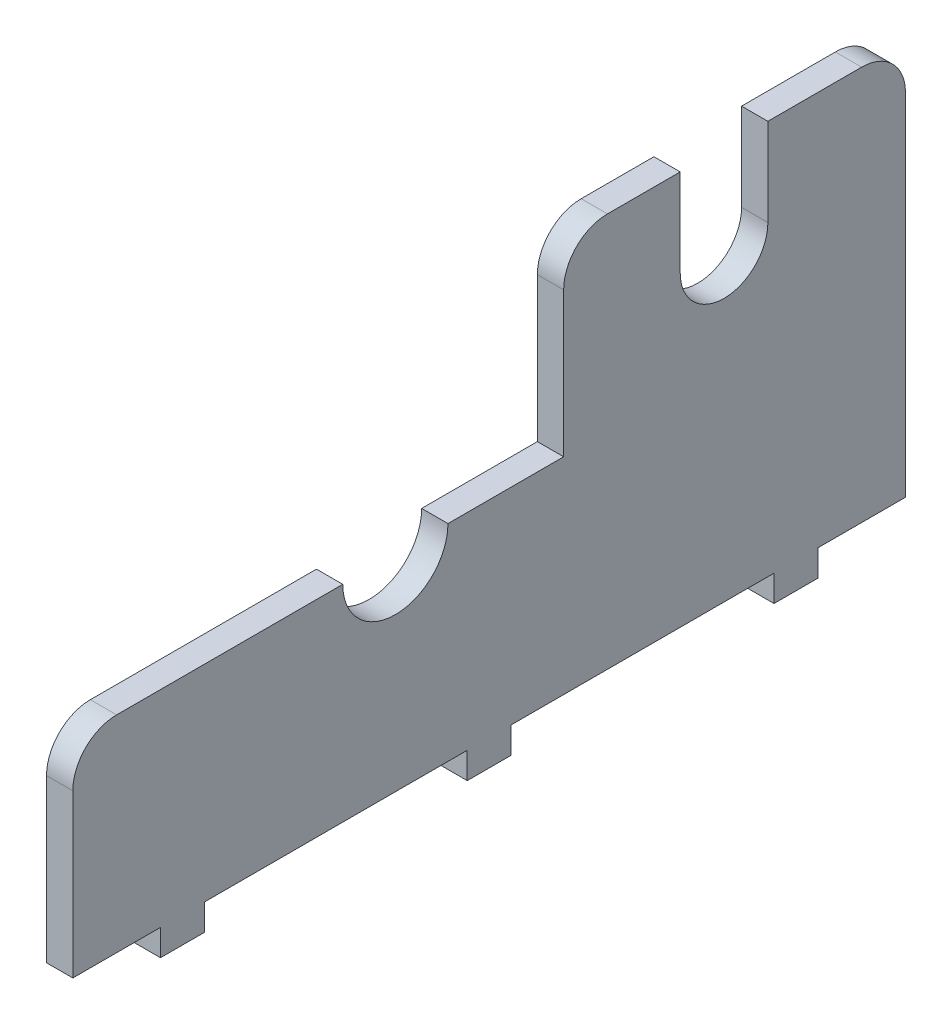
SolidWorks part; units mm, degrees
ref_plane "Front Plane" through (0, 0, 0) normal (0, 0, 1) x (1, 0, 0)
ref_plane "Top Plane" through (0, 0, 0) normal (0, 1, 0) x (1, 0, 0)
ref_plane "Right Plane" through (0, 0, 0) normal (1, 0, 0) x (0, 0, -1)
sketch "Sketch1" plane through (0, 0, 0) normal (1, 0, 0) x (0, 0, -1)
  line L0 (0, 55) -> (0, -55) construction
  line L1 (65, 0) -> (-30, 0)
  line L2 (65, 0) -> (65, 23.5)
  line L3 (65, 23.5) -> (-30, 23.5)
  line L4 (-30, 0) -> (-30, 23.5)
  line L5 (55, 0) -> (-55, 0) construction
  point P0 (0, 0)
  dimension "D2" = 30
  dimension "D1" = 95
  dimension "D4" = 23.5
extrude "Boss-Extrude1" add sketch "Sketch1" along normal blind 3
sketch "Sketch2" plane through (3, 0, 0) normal (1, 0, 0) x (0, 0, -1)
  line L0 (-30, 0) -> (65, 0) construction
  line L7 (-26.9862, 0) -> (-28.4862, -10) construction
  circle A0 centre (6.8, 23.5) radius 6
  point P6 (-28.4862, -10)
  point P11 (28.0724, -10)
  dimension "D1" = 12
  dimension "D3" = 6.8
  dimension "D2" = 23.5
extrude "Cut-Extrude1" cut sketch "Sketch2" against normal through all
sketch "Sketch4" plane through (0, 0, 0) normal (0, -1, 0) x (1, 0, 0)
  line L0 (3, 30) -> (3, -65) construction
  line L1 (3, 20) -> (0, 20)
  line L2 (3, 20) -> (3, 15)
  line L3 (3, 15) -> (0, 15)
  line L4 (0, 20) -> (0, 15)
  line L5 (0, 30) -> (0, -65) construction
  line L6 (3, 30) -> (0, 30) construction
  dimension "D1" = 5
  dimension "D2" = 10
extrude "Boss-Extrude2" add sketch "Sketch4" along normal blind 3
sketch "Sketch9" plane through (0, 23.5, 0) normal (0, 1, 0) x (1, 0, 0)
  line L0 (3, -30) -> (0, -30) construction
  line L1 (0, 26) -> (3, 26)
  line L2 (0, 26) -> (0, 65)
  line L3 (0, 65) -> (3, 65)
  line L4 (3, 26) -> (3, 65)
  dimension "D1" = 39
  dimension "D2" = 56
extrude "Boss-Extrude5" add sketch "Sketch9" along normal blind 21.5
sketch "Sketch10" plane through (3, 0, 0) normal (1, 0, 0) x (0, 0, -1)
  line L0 (1.65, 0) -> (-1.65, 0) construction
  line L2 (39.3, 35) -> (39.3, 45)
  line L3 (26, 45) -> (65, 45) construction
  line L4 (39.3, 45) -> (49.3, 45)
  line L5 (49.3, 45) -> (49.3, 35)
  line L6 (-30, 23.5) -> (-30, 0) construction
  arc A0 (39.3, 35) -> (49.3, 35) centre (44.3, 35) ccw
  dimension "D1" = 10
  dimension "D2" = 35
  dimension "D3" = 74.3
extrude "Cut-Extrude5" cut sketch "Sketch10" against normal through all
fillet "Fillet5" radius 5 3 edges at (1.5, 45, -65) (1.5, 45, -26) (1.5, 23.5, 30)
pattern_linear "LPattern1" count 3 spacing 35 along (0, 0, -1) of "Boss-Extrude2"
